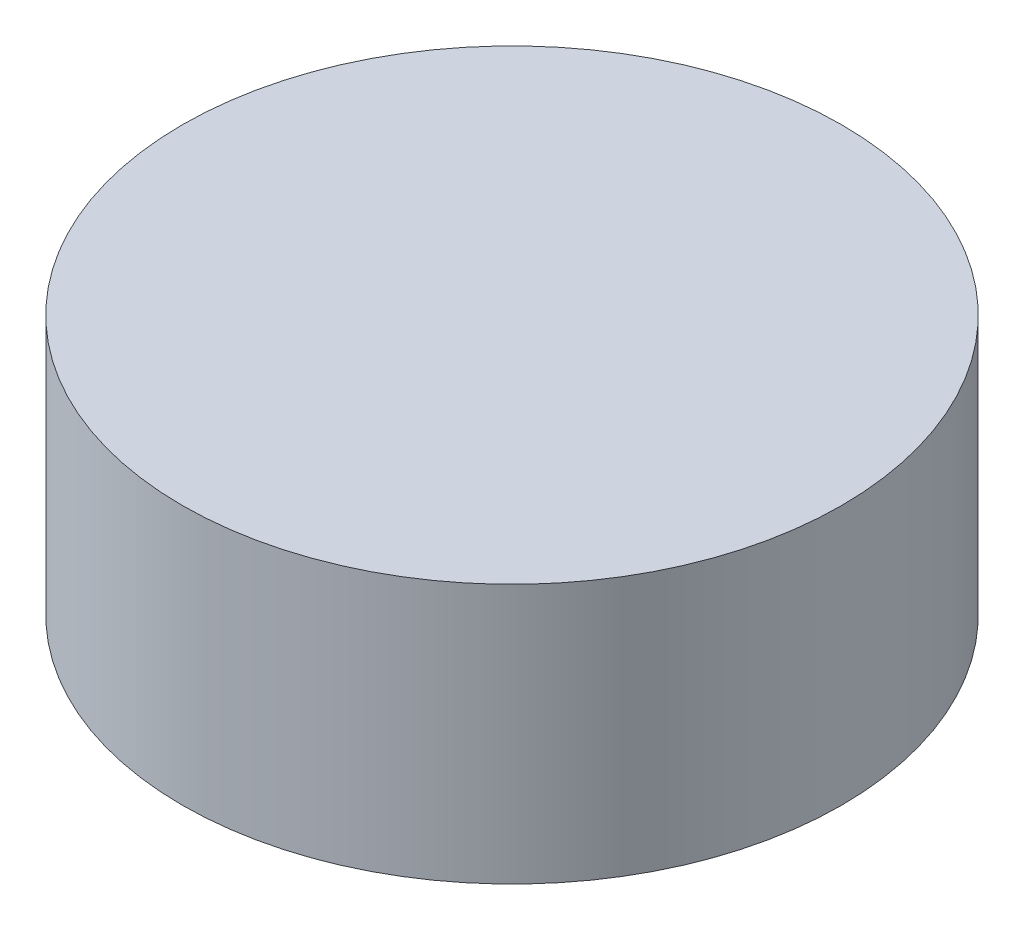
SolidWorks part; units mm, degrees
ref_plane "Front Plane" through (0, 0, 0) normal (0, 0, 1) x (1, 0, 0)
ref_plane "Top Plane" through (0, 0, 0) normal (0, 1, 0) x (1, 0, 0)
ref_plane "Right Plane" through (0, 0, 0) normal (1, 0, 0) x (0, 0, -1)
sketch "Sketch1" plane through (0, 0, 0) normal (0, 1, 0) x (1, 0, 0)
  circle A0 centre (0, 0) radius 12.7
  dimension "D1" = 25.4
extrude "Boss-Extrude1" add sketch "Sketch1" along normal blind 10 contours A0
